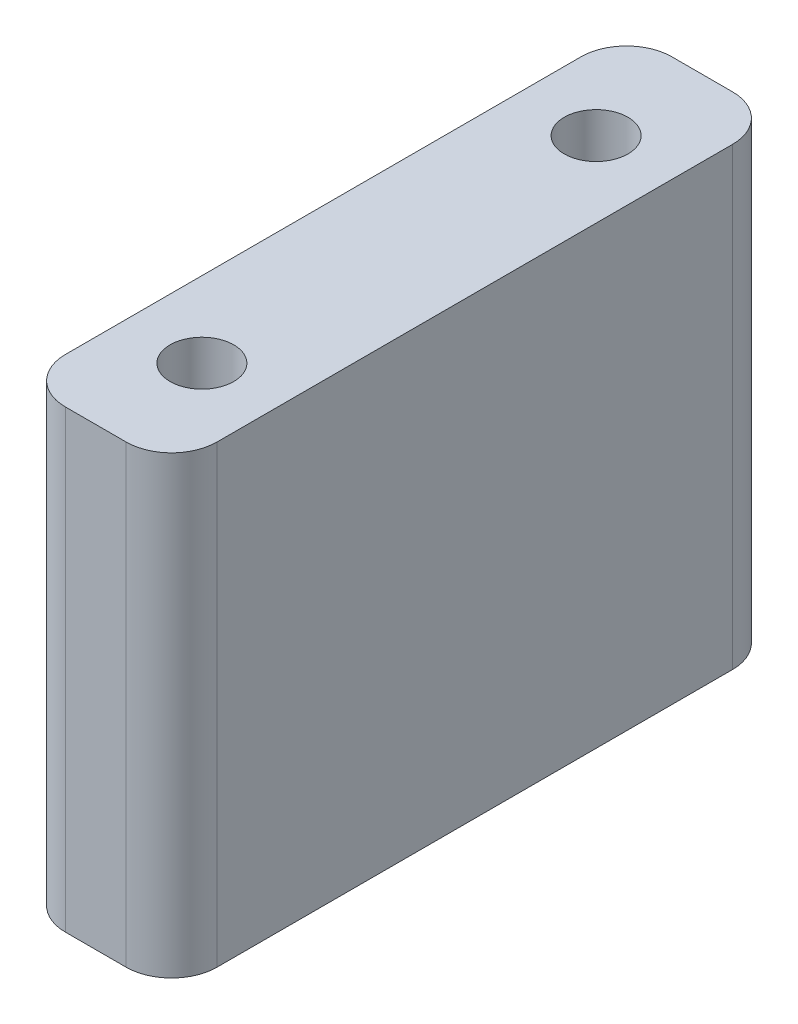
SolidWorks part; units mm, degrees
ref_plane "前视基准面" through (0, 0, 0) normal (0, 0, 1) x (1, 0, 0)
ref_plane "上视基准面" through (0, 0, 0) normal (0, 1, 0) x (1, 0, 0)
ref_plane "右视基准面" through (0, 0, 0) normal (1, 0, 0) x (0, 0, -1)
sketch "草图1" plane through (0, 0, 0) normal (0, 1, 0) x (1, 0, 0)
  line L5 (-10, 0) -> (0, 0)
  line L6 (-10, 0) -> (-10, -40)
  line L7 (-10, -40) -> (0, -40)
  line L8 (0, 0) -> (0, -40)
  circle A2 centre (-5, -7) radius 2.1
  circle A3 centre (-5, -33) radius 2.1
  point P18 (-10, -20)
  dimension "D5" = 0
  dimension "D8" = 26
  dimension "D9" = 13
  dimension "D10" = 4.2
  dimension "D11" = 4.2
  dimension "D16" = 5
  dimension "D17" = 5
  dimension "D2" = 0
  dimension "D3" = 10
  dimension "D4" = 40
extrude "凸台-拉伸1" add sketch "草图1" along normal blind 30
fillet "圆角1" radius 3 4 edges at (-10, 15, 40) (0, 15, 40) (0, 15, 0) (-10, 15, 0)
